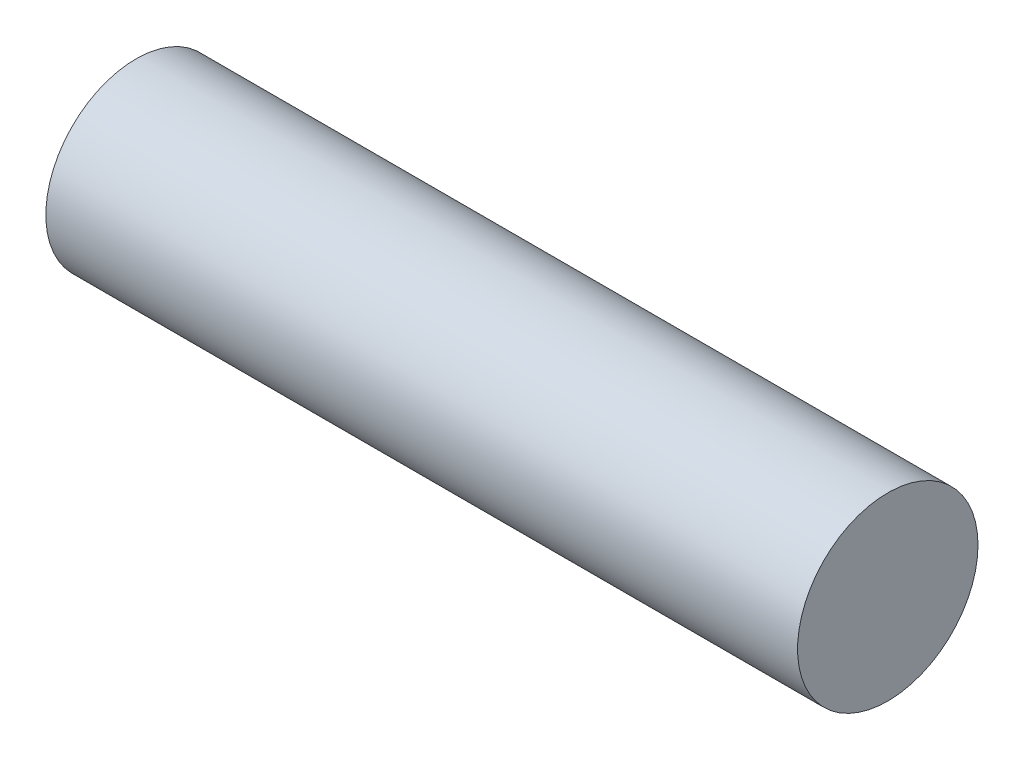
SolidWorks part; units mm, degrees
ref_plane "Front Plane" through (0, 0, 0) normal (0, 0, 1) x (1, 0, 0)
ref_plane "Top Plane" through (0, 0, 0) normal (0, 1, 0) x (1, 0, 0)
ref_plane "Right Plane" through (0, 0, 0) normal (1, 0, 0) x (0, 0, -1)
sketch "Sketch1" plane through (0, 0, 0) normal (1, 0, 0) x (0, 0, -1)
  circle A0 centre (0, 0) radius 3
  dimension "D1" = 6
extrude "Boss-Extrude1" add sketch "Sketch1" along normal blind 25
